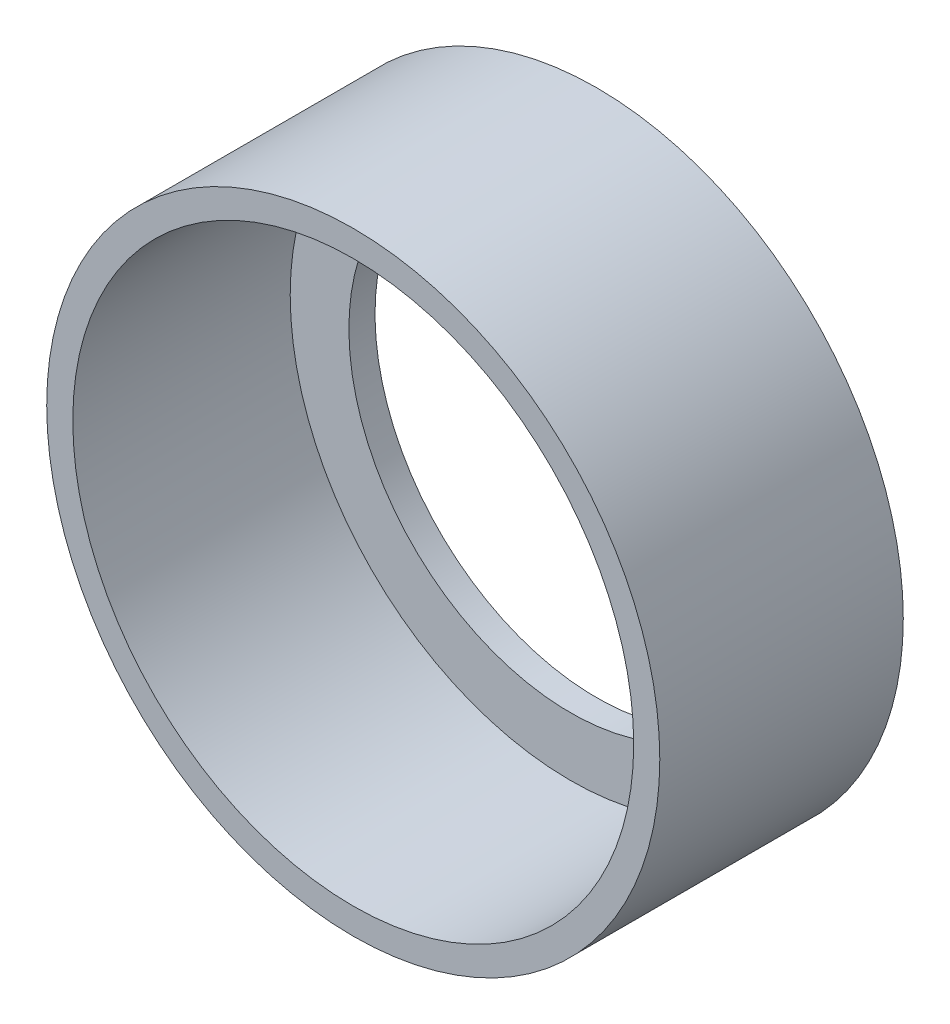
SolidWorks part; units mm, degrees
ref_plane "Front Plane" through (0, 0, 0) normal (0, 0, 1) x (1, 0, 0)
ref_plane "Top Plane" through (0, 0, 0) normal (0, 1, 0) x (1, 0, 0)
ref_plane "Right Plane" through (0, 0, 0) normal (1, 0, 0) x (0, 0, -1)
sketch "Sketch1" plane through (0, 0, 0) normal (0, 1, 0) x (1, 0, 0)
  line L0 (0, 10.179) -> (0, 0) construction
  line L1 (16.383, 5.4256) -> (17.907, 5.4256)
  line L2 (17.907, 5.4256) -> (17.907, 19.6496)
  line L3 (17.907, 19.6496) -> (12.954, 19.6496)
  line L4 (12.954, 19.6496) -> (12.954, 18.1256)
  line L5 (12.954, 18.1256) -> (16.383, 18.1256)
  line L6 (16.383, 18.1256) -> (16.383, 5.4256)
  dimension "D1" = 1.524
  dimension "D2" = 16.383
  dimension "D3" = 12.954
  dimension "D4" = 1.524
  dimension "D5" = 12.7
  dimension "D6" = 3.429
revolve "Revolve1" add sketch "Sketch1" angle 360 about L0
sketch "Sketch2" plane through (0, 0, -19.6496) normal (0, 0, -1) x (-1, 0, 0)
  line L2 (-4.8895, 15.6364) -> (-4.8895, 10.5564)
  line L3 (-4.8895, 10.5564) -> (4.8895, 10.5564)
  line L4 (4.8895, 15.6364) -> (4.8895, 10.5564)
  arc A0 (-4.8895, 15.6364) -> (4.8895, 15.6364) centre (0, 0) cw
  point P7 (0, 10.5564)
  point P8 (2.9104, 16.1849)
  dimension "D1" = 16.383
  dimension "D2" = 9.779
  dimension "D3" = 5.08
extrude "Cut-Extrude1" cut sketch "Sketch2" against normal through all
